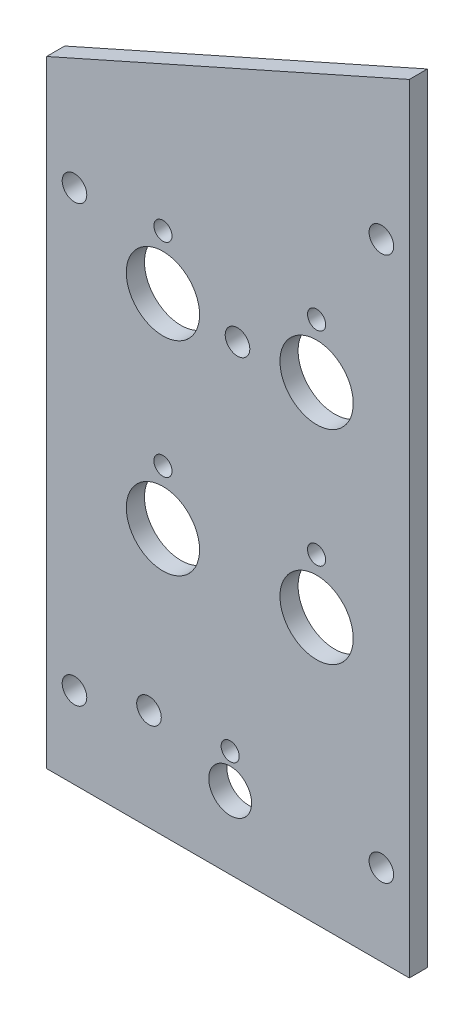
SolidWorks part; units mm, degrees
material "PET"
ref_plane "Front Plane" through (0, 0, 0) normal (0, 0, 1) x (1, 0, 0)
ref_plane "Top Plane" through (0, 0, 0) normal (0, 1, 0) x (1, 0, 0)
ref_plane "Right Plane" through (0, 0, 0) normal (1, 0, 0) x (0, 0, -1)
sketch "Sketch1" plane through (0, 0, 0) normal (0, 0, 1) x (1, 0, 0)
  line L4 (0, 107.95) -> (0, 0)
  line L5 (0, 0) -> (63.5, 0)
  line L6 (63.5, 0) -> (63.5, 136.2202)
  line L7 (63.5, 136.2202) -> (0, 107.95)
  line L8 (0, 107.95) -> (0, 0)
  line L9 (0, 0) -> (63.5, 0)
  line L10 (63.5, 0) -> (63.5, 136.2202)
  line L11 (63.5, 136.2202) -> (0, 107.95)
  dimension "D1" = 0
extrude "Boss-Extrude1" add sketch "Sketch1" against normal blind 3.175
hole_wizard "#6 Clearance Hole1" positions "Sketch4" profile "Sketch3" hole size "#6" standard "ANSI Inch" end condition through all
sketch "Sketch4" plane through (0, 0, 0) normal (0, 0, 1) x (1, 0, 0)
  point P0 (58.6105, 14.2875)
  point P3 (4.8895, 14.2875)
  point P6 (4.8895, 90.4875)
  point P9 (58.6105, 109.5375)
sketch "Sketch3" plane through (58.6105, 14.2875, 0) normal (1, 0, 0) x (0, -1, 0)
  line L0 (0, 0) -> (0, 3.175)
  line L1 (0, 3.175) -> (2.1526, 3.175)
  line L2 (2.1526, 3.175) -> (2.1526, 0)
  line L5 (2.1526, 0) -> (0, 0)
  line L11 (0, -6.35) -> (0, 107.95) construction
  dimension "Thru Hole Dia." = 4.3053
  dimension "Thru Hole Depth" = 3.175
sketch "Sketch8" plane through (0, 0, 0) normal (0, 0, 1) x (1, 0, 0)
  line L0 (0, 0) -> (63.5, 0) construction
  line L1 (20.3732, 91.7104) -> (20.3732, 82.1854) construction
  line L2 (20.3732, 56.073) -> (20.3732, 46.548) construction
  line L3 (47.2705, 46.548) -> (47.2705, 56.073) construction
  line L4 (32.1439, 18.7) -> (32.1439, 12.7) construction
  line L5 (81.6444, 34.0155) -> (81.6444, 24.4905) construction
  line L6 (47.2705, 82.1854) -> (47.2705, 91.7104) construction
  line L7 (0, 107.95) -> (0, 0) construction
  circle A1 centre (20.3732, 91.7104) radius 1.5875
  circle A2 centre (47.2705, 91.7104) radius 1.5875
  circle A3 centre (47.2705, 56.073) radius 1.5875
  circle A4 centre (32.1439, 12.7) radius 3.75
  circle A5 centre (20.3732, 56.073) radius 1.5875
  circle A6 centre (32.1439, 18.7) radius 1.5875
  circle A10 centre (47.2705, 46.548) radius 6.4135
  circle A12 centre (47.2705, 82.1854) radius 6.4135
  circle A15 centre (20.3732, 82.1854) radius 6.4135
  circle A17 centre (20.3732, 46.548) radius 6.4135
  circle A18 centre (81.6444, 34.0155) radius 1.651 construction
  circle A19 centre (81.6444, 24.4905) radius 6.4135 construction
  dimension "D2" = 26.8973
  dimension "D3" = 12.827
  dimension "D9" = 3.175
  dimension "D10" = 3.175
  dimension "D11" = 3.175
  dimension "D12" = 3.175
  dimension "D13" = 3.175
  dimension "D14" = 7.5
  dimension "D1" = 9.525
  dimension "D4" = 35.6374
  dimension "D5" = 33.848
  dimension "D6" = 15.1266
  dimension "D7" = 12.7
  dimension "D8" = 32.1439
  dimension "D15" = 6
extrude "Cut-Extrude1" cut sketch "Sketch8" against normal through all
hole_wizard "#6 Clearance Hole2" positions "Sketch9" profile "Sketch10" hole size "#6" standard "ANSI Inch" end condition through all
sketch "Sketch9" plane through (31.75, 0, 6.35) normal (0, 0, 1) x (1, 0, 0)
  point P0 (1.6763, 81.3834)
  point P2 (-13.8187, 17.7712)
  point P3 (2.5973, 88.3171)
  point P4 (1.6763, 81.3834)
sketch "Sketch10" plane through (33.4263, 81.3834, 6.35) normal (1, 0, 0) x (0, -1, 0)
  line L0 (0, 0) -> (0, 9.525)
  line L1 (0, 9.525) -> (2.1526, 9.525)
  line L2 (2.1526, 9.525) -> (2.1526, 0)
  line L3 (2.1526, 0) -> (0, 0)
  line L4 (0, -6.35) -> (0, 107.95) construction
  dimension "Thru Hole Dia." = 4.3053
  dimension "Thru Hole Depth" = 9.525
